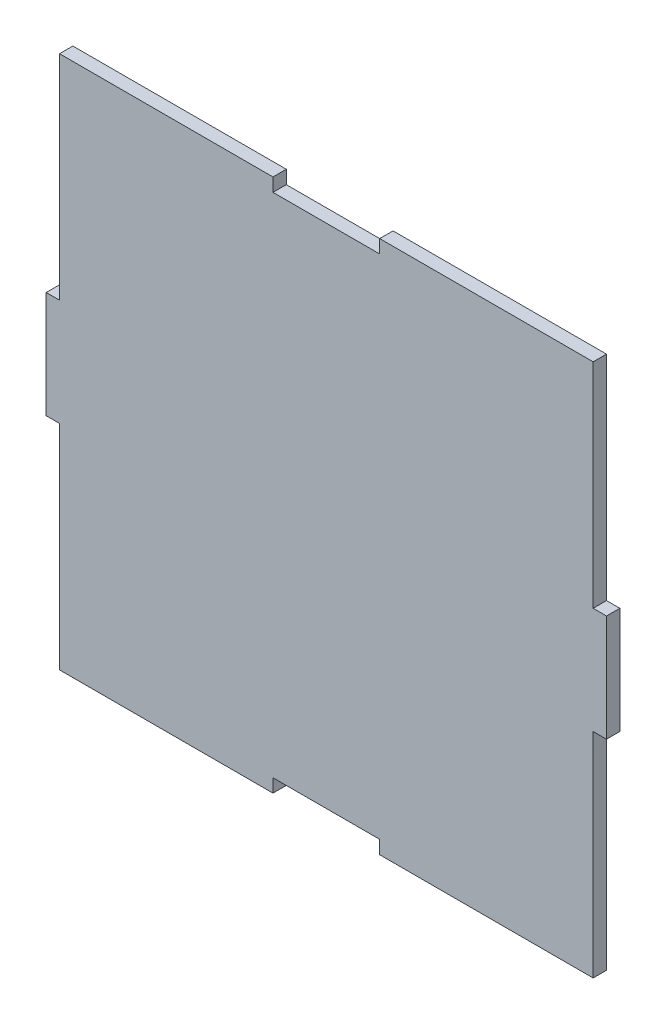
SolidWorks part; units mm, degrees
ref_plane "Alzado" through (0, 0, 0) normal (0, 0, 1) x (1, 0, 0)
ref_plane "Planta" through (0, 0, 0) normal (0, 1, 0) x (1, 0, 0)
ref_plane "Vista lateral" through (0, 0, 0) normal (1, 0, 0) x (0, 0, -1)
sketch "Croquis1" plane through (0, 0, 0) normal (0, 0, 1) x (1, 0, 0)
  line L0 (0, 0) -> (100, 0) construction
  line L2 (-100, -100) -> (-100, -20)
  line L3 (-100, 100) -> (-20, 100)
  line L5 (-100, -100) -> (100, 100) construction
  line L6 (-100, 100) -> (100, -100) construction
  line L8 (-20, 100) -> (-20, 95)
  line L9 (-20, 95) -> (20, 95)
  line L10 (20, 100) -> (20, 95)
  line L11 (20, 100) -> (100, 100)
  line L12 (20, -100) -> (100, -100)
  line L13 (20, -100) -> (20, -95)
  line L14 (-20, -95) -> (20, -95)
  line L15 (-20, -100) -> (-20, -95)
  line L16 (-100, -100) -> (-20, -100)
  line L17 (-100, 20) -> (-100, 100)
  line L18 (-100, 20) -> (-105, 20)
  line L20 (-100, -20) -> (-105, -20)
  line L21 (-105, 20) -> (-105, -20)
  line L22 (0, 0) -> (0, 42.2428) construction
  line L23 (105, 20) -> (105, -20)
  line L24 (100, -20) -> (105, -20)
  line L25 (100, 20) -> (105, 20)
  line L26 (100, 20) -> (100, 100)
  line L27 (100, -100) -> (100, -20)
  point P0 (0, 0)
  dimension "D1" = 200
  dimension "D2" = 200
  dimension "D3" = 5
  dimension "D4" = 40
  dimension "D5" = 5
  dimension "D6" = 40
extrude "Saliente-Extruir1" add sketch "Croquis1" along normal blind 5
